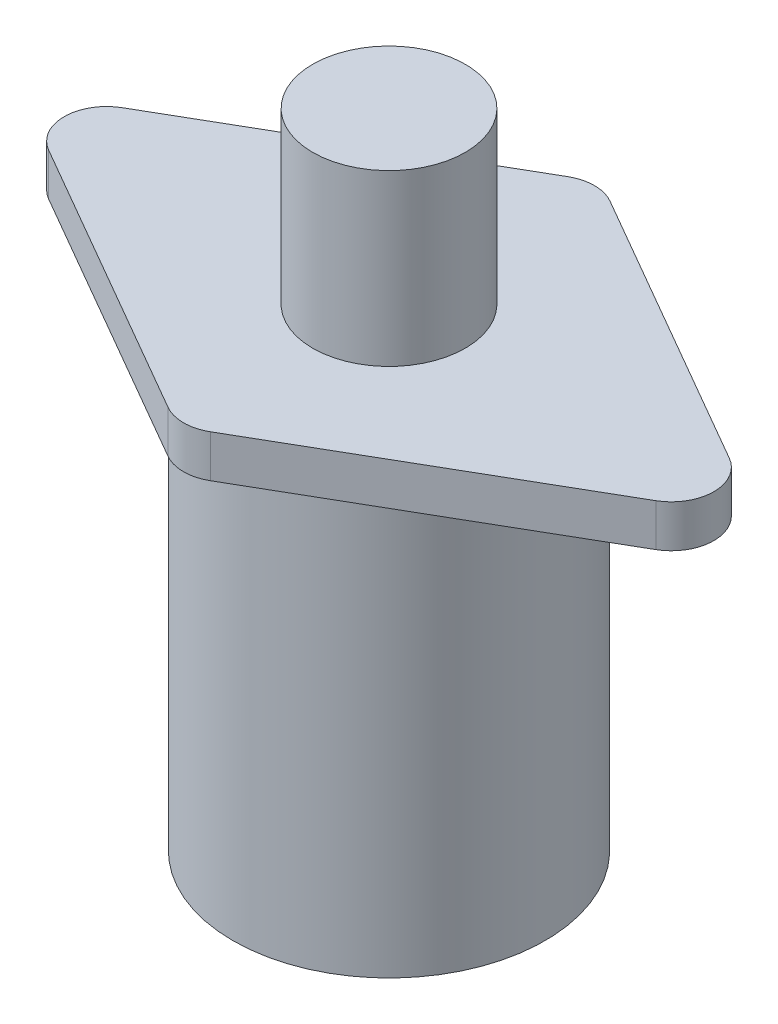
SolidWorks part; units mm, degrees
ref_plane "Alzado" through (0, 0, 0) normal (0, 0, 1) x (1, 0, 0)
ref_plane "Planta" through (0, 0, 0) normal (0, 1, 0) x (1, 0, 0)
ref_plane "Vista lateral" through (0, 0, 0) normal (1, 0, 0) x (0, 0, -1)
sketch "Sketch1" plane through (0, 0, 0) normal (0, 1, 0) x (1, 0, 0)
  circle A0 centre (0, 0) radius 18.4
  dimension "D1" = 36.8
extrude "Boss-Extrude1" add sketch "Sketch1" along normal blind 50.8
sketch "Sketch2" plane through (0, 50.8, 0) normal (0, 1, 0) x (1, 0, 0)
  line L0 (0, 25) -> (0, -25) construction
  line L1 (0, 25) -> (-43.3013, 0)
  line L2 (-43.3013, 0) -> (0, -25)
  line L3 (0, -25) -> (43.3013, 0)
  line L4 (43.3013, 0) -> (0, 25)
  point P3 (0, 26.3159)
  point P6 (0, 0)
  dimension "D1" = 50
extrude "Boss-Extrude2" add sketch "Sketch2" along normal blind 5
fillet "Fillet1" radius 5 4 edges at (0, 53.3, -25) (0, 53.3, 25) (43.3013, 53.3, 0) (-43.3013, 53.3, 0)
sketch "Sketch3" plane through (0, 55.8, 0) normal (0, 1, 0) x (1, 0, 0)
  circle A0 centre (0, 0) radius 9
  dimension "D1" = 18
extrude "Boss-Extrude3" add sketch "Sketch3" along normal blind 20
